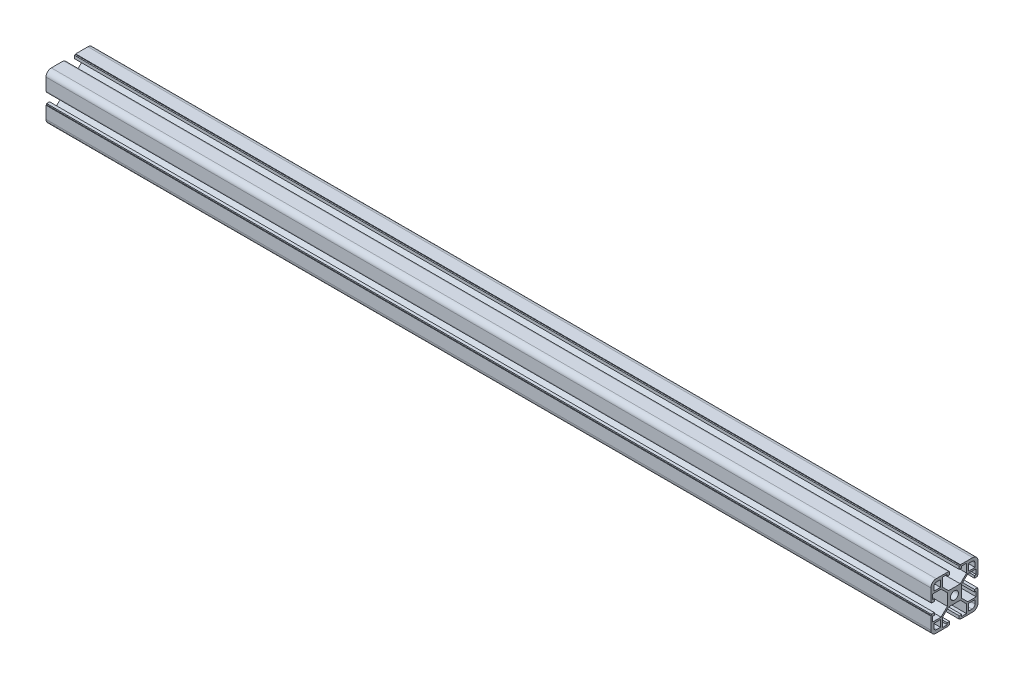
SolidWorks part; units mm, degrees
ref_plane "前视基准面" through (0, 0, 0) normal (0, 0, 1) x (1, 0, 0)
ref_plane "上视基准面" through (0, 0, 0) normal (0, 1, 0) x (1, 0, 0)
ref_plane "右视基准面" through (0, 0, 0) normal (1, 0, 0) x (0, 0, -1)
sketch "草图1" plane through (0, 0, 0) normal (0, 1, 0) x (1, 0, 0)
  line L0 (-244.7968, 0) -> (505.2032, 0)
  dimension "D1" = 750
other "铝型材 40 X 40L X R4.5(1)"
ref_plane "基准面1" through (-244.7968, 0, 0) normal (1, 0, 0) x (0, 0, -1)
sketch "Sketch1" plane through (-244.7968, 0, 0) normal (1, 0, 0) x (0, 0, -1)
  line L0 (-5.1, 20) -> (-5.1, 19.5)
  line L1 (-5.1, 19.5) -> (-4.1, 19.5)
  line L2 (-4.1, 19.5) -> (-4.1, 17)
  line L3 (-6.1, 18.5) -> (-10.3, 18.5)
  line L4 (-15.5, -20) -> (-5.1, -20)
  line L5 (-20, -15.5) -> (-20, -5.1)
  line L6 (15.5, 20) -> (5.1, 20)
  line L7 (20, 15.5) -> (20, 5.1)
  line L8 (0, 14.8756) -> (0, 0) construction
  line L9 (0, 0) -> (14.1675, 0) construction
  line L10 (-10.3, 18.5) -> (-10.3, 11.3)
  line L11 (-10.3, 11.3) -> (-5, 6)
  line L12 (-5, 6) -> (5, 6)
  line L13 (10.3, 11.3) -> (5, 6)
  line L14 (10.3, 18.5) -> (10.3, 11.3)
  line L15 (6.1, 18.5) -> (10.3, 18.5)
  line L16 (4.1, 19.5) -> (4.1, 17)
  line L17 (5.1, 19.5) -> (4.1, 19.5)
  line L18 (5.1, 20) -> (5.1, 19.5)
  line L19 (-5.1, 20) -> (-15.5, 20)
  line L20 (20, 5.1) -> (19.5, 5.1)
  line L21 (11.8, 17.5) -> (15, 17.5)
  line L22 (11.8, 17.5) -> (11.8, 11.8)
  line L23 (11.8, 11.8) -> (17.5, 11.8)
  line L24 (17.5, 15) -> (17.5, 11.8)
  line L25 (19.5, 5.1) -> (19.5, 4.1)
  line L26 (19.5, 4.1) -> (17, 4.1)
  line L27 (17, 6.1) -> (17, 4.1)
  line L28 (18.5, 6.1) -> (17, 6.1)
  line L29 (18.5, 6.1) -> (18.5, 10.3)
  line L30 (18.5, 10.3) -> (11.3, 10.3)
  line L31 (11.3, 10.3) -> (6, 5)
  line L32 (6, 5) -> (6, -5)
  line L33 (11.3, -10.3) -> (6, -5)
  line L34 (18.5, -10.3) -> (11.3, -10.3)
  line L35 (18.5, -6.1) -> (18.5, -10.3)
  line L36 (18.5, -6.1) -> (17, -6.1)
  line L37 (17, -4.1) -> (17, -6.1)
  line L38 (19.5, -4.1) -> (17, -4.1)
  line L39 (19.5, -5.1) -> (19.5, -4.1)
  line L40 (20, -5.1) -> (19.5, -5.1)
  line L41 (5.1, -20) -> (5.1, -19.5)
  line L42 (5.1, -19.5) -> (4.1, -19.5)
  line L43 (4.1, -19.5) -> (4.1, -17)
  line L44 (6.1, -17) -> (4.1, -17)
  line L45 (6.1, -18.5) -> (6.1, -17)
  line L46 (6.1, -18.5) -> (10.3, -18.5)
  line L47 (10.3, -18.5) -> (10.3, -11.3)
  line L48 (10.3, -11.3) -> (5, -6)
  line L49 (5, -6) -> (-5, -6)
  line L50 (-10.3, -11.3) -> (-5, -6)
  line L51 (-10.3, -18.5) -> (-10.3, -11.3)
  line L52 (-6.1, -18.5) -> (-10.3, -18.5)
  line L53 (-6.1, -18.5) -> (-6.1, -17)
  line L54 (-4.1, -17) -> (-6.1, -17)
  line L55 (-4.1, -19.5) -> (-4.1, -17)
  line L56 (-5.1, -19.5) -> (-4.1, -19.5)
  line L57 (-5.1, -20) -> (-5.1, -19.5)
  line L58 (-20, -5.1) -> (-19.5, -5.1)
  line L59 (5.1, -20) -> (15.5, -20)
  line L60 (-20, 5.1) -> (-20, 15.5)
  line L61 (-19.5, -5.1) -> (-19.5, -4.1)
  line L62 (-6.1, 18.5) -> (-6.1, 17)
  line L63 (-6.1, 17) -> (-4.1, 17)
  line L64 (6.1, 18.5) -> (6.1, 17)
  line L65 (4.1, 17) -> (6.1, 17)
  line L66 (-19.5, -4.1) -> (-17, -4.1)
  line L67 (-15, 17.5) -> (-11.8, 17.5)
  line L68 (-17.5, 15) -> (-17.5, 11.8)
  line L69 (-17.5, 11.8) -> (-11.8, 11.8)
  line L70 (-11.8, 17.5) -> (-11.8, 11.8)
  line L71 (-17, -6.1) -> (-17, -4.1)
  line L72 (-18.5, -6.1) -> (-17, -6.1)
  line L73 (-18.5, -6.1) -> (-18.5, -10.3)
  line L74 (-18.5, -10.3) -> (-11.3, -10.3)
  line L75 (-11.3, -10.3) -> (-6, -5)
  line L76 (-6, -5) -> (-6, 5)
  line L77 (-11.3, 10.3) -> (-6, 5)
  line L78 (-18.5, 10.3) -> (-11.3, 10.3)
  line L79 (-18.5, 6.1) -> (-18.5, 10.3)
  line L80 (-18.5, 6.1) -> (-17, 6.1)
  line L81 (-17, 4.1) -> (-17, 6.1)
  line L82 (-19.5, 4.1) -> (-17, 4.1)
  line L83 (-19.5, 5.1) -> (-19.5, 4.1)
  line L84 (-20, 5.1) -> (-19.5, 5.1)
  line L85 (20, -5.1) -> (20, -15.5)
  line L87 (-17.5, -11.8) -> (-11.8, -11.8)
  line L88 (-17.5, -11.8) -> (-17.5, -15)
  line L89 (-15, -17.5) -> (-11.8, -17.5)
  line L90 (-11.8, -11.8) -> (-11.8, -17.5)
  line L91 (11.8, -11.8) -> (17.5, -11.8)
  line L92 (11.8, -11.8) -> (11.8, -17.5)
  line L93 (11.8, -17.5) -> (15, -17.5)
  line L94 (17.5, -11.8) -> (17.5, -15)
  circle A0 centre (0, 0) radius 3.4
  arc A1 (-20, 15.5) -> (-15.5, 20) centre (-15.5, 15.5) cw
  arc A2 (20, 15.5) -> (15.5, 20) centre (15.5, 15.5) ccw
  arc A3 (-15.5, -20) -> (-20, -15.5) centre (-15.5, -15.5) cw
  arc A4 (15.5, -20) -> (20, -15.5) centre (15.5, -15.5) ccw
  arc A5 (-15, 17.5) -> (-17.5, 15) centre (-15, 15) ccw
  arc A6 (17.5, 15) -> (15, 17.5) centre (15, 15) ccw
  arc A7 (17.5, -15) -> (15, -17.5) centre (15, -15) cw
  arc A8 (-17.5, -15) -> (-15, -17.5) centre (-15, -15) ccw
  point P2 (0, 10)
  point P4 (0, 0)
  point P5 (-20, -20)
  point P6 (20, -20)
  point P7 (20, 20)
  point P8 (-20, 20)
  point P36 (-20, 20)
  point P39 (20, 20)
  point P121 (0, 0)
  dimension "D1" = 20.6
  dimension "D2" = 40
  dimension "D3" = 8.2
  dimension "D4" = 10.2
  dimension "D5" = 14
  dimension "D6" = 6.8
  dimension "D7" = 4.5
  dimension "D8" = 45
  dimension "D12" = 2.5
  dimension "D13" = 5.7
  dimension "D14" = 1.5
  dimension "D18" = 2.5
  dimension "D19" = 2.5
  dimension "D15" = 2.5
  dimension "D9" = 0.5
  dimension "D10" = 1.5
  dimension "D11" = 10
  dimension "D16" = 3
  dimension "D17" = 2
  dimension "D20" = 1.5
  dimension "D21" = 2.5
